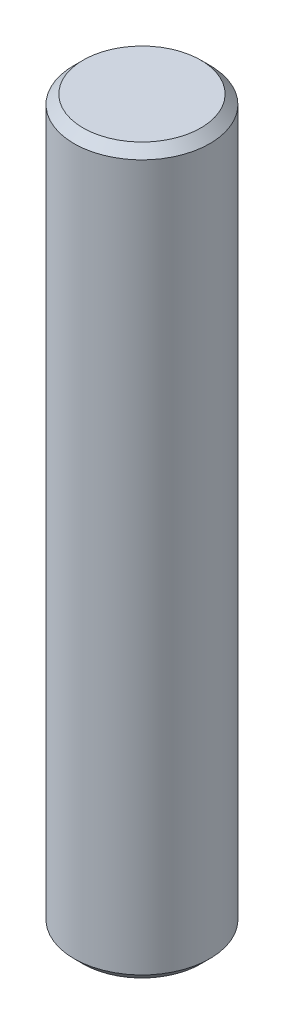
SolidWorks part; units mm, degrees
material "普通碳钢"
ref_plane "前视基准面" through (0, 0, 0) normal (0, 0, 1) x (1, 0, 0)
ref_plane "上视基准面" through (0, 0, 0) normal (0, 1, 0) x (1, 0, 0)
ref_plane "右视基准面" through (0, 0, 0) normal (1, 0, 0) x (0, 0, -1)
sketch "草图1" plane through (0, 0, 0) normal (0, 1, 0) x (1, 0, 0)
  circle A0 centre (0, 0) radius 1.5
  dimension "D1" = 3
extrude "凸台-拉伸1" add sketch "草图1" along normal blind 16
chamfer "倒角1" distance 0.2 angle 45 2 edges at (0, 16, 1.5) (0, 0, 1.5)
